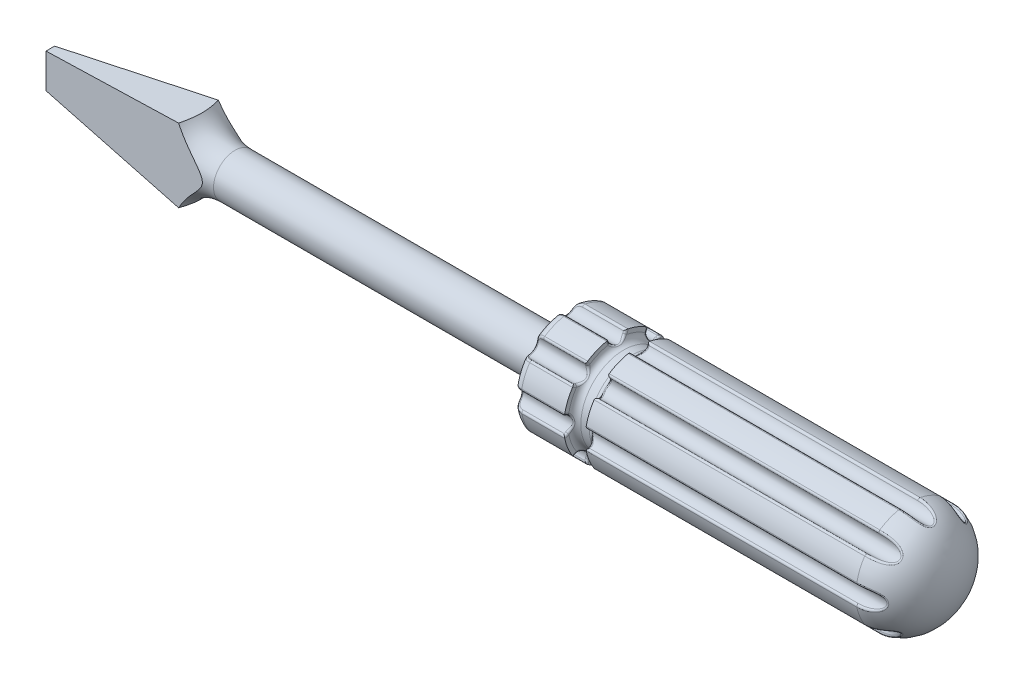
SolidWorks part; units mm, degrees
ref_plane "Front Plane" through (0, 0, 0) normal (0, 0, 1) x (1, 0, 0)
ref_plane "Top Plane" through (0, 0, 0) normal (0, 1, 0) x (1, 0, 0)
ref_plane "Right Plane" through (0, 0, 0) normal (1, 0, 0) x (0, 0, -1)
sketch "Sketch1" plane through (0, 0, 0) normal (0, 0, 1) x (1, 0, 0)
  line L0 (0, 0) -> (0, 8711.6046) construction
  line L1 (0, 0) -> (8711.6046, 0) construction
  line L2 (0, 0) -> (0, 5.25)
  line L3 (1, 6.25) -> (6, 6.25)
  line L4 (6, 6.25) -> (6, 5.75)
  line L5 (6.75, 5) -> (7.75, 5)
  line L6 (8.5, 5.75) -> (8.5, 6.25)
  line L7 (8.5, 6.25) -> (40, 6.25)
  line L8 (0, 0) -> (45, 0)
  arc A0 (7.75, 5) -> (8.5, 5.75) centre (7.75, 5.75) ccw
  arc A1 (6.75, 5) -> (6, 5.75) centre (6.75, 5.75) cw
  arc A2 (0, 5.25) -> (1, 6.25) centre (1, 5.25) cw
  ellipse E0 centre (40, 0) end of major axis (40, 6.25) minor radius 5 (45, 0) -> (40, 6.25) ccw
  point P20 (8.5, 5)
  point P23 (6, 5)
  point P26 (0, 6.25)
  dimension "D7" = 0.75
  dimension "D8" = 1
  dimension "D1" = 12.5
  dimension "D2" = 10
  dimension "D3" = 6
  dimension "D4" = 2.5
  dimension "D5" = 5
  dimension "D6" = 45
revolve "Revolve1" add sketch "Sketch1" angle 360 about L1
sketch "Sketch2" plane through (0, 0, 0) normal (-1, 0, 0) x (0, 0, 1)
  circle A0 centre (0, 0) radius 2.5
  dimension "D1" = 5
extrude "Boss-Extrude1" add sketch "Sketch2" along normal blind 43.5
sketch "Sketch3" plane through (0, 0, 0) normal (0, 0, 1) x (1, 0, 0)
  line L0 (0, 0) -> (-75.7303, 0) construction
  line L1 (0, 5.25) -> (0, -5.25) construction
  line L2 (-43.5, 2.5) -> (-43.5, -2.5) construction
  line L3 (-43.5, 8.25) -> (-60, 8.25)
  line L4 (-43.5, 8.25) -> (-43.5, -8.25)
  line L5 (-43.5, -8.25) -> (-60, -8.25)
  line L6 (-60, 8.25) -> (-60, -8.25)
  dimension "D1" = 16.5
extrude "Boss-Extrude2" add sketch "Sketch3" along normal mid plane 16.5
fillet "Fillet1" radius 5 1 edges at (-43.5, 0, 2.5)
sketch "Sketch4" plane through (0, 0, 8.25) normal (0, 0, 1) x (1, 0, 0)
  line L0 (-60, 0) -> (-50060, 0) construction
  line L1 (-60, 8.25) -> (-60, -8.25) construction
  line L2 (-60.0153, 0) -> (-60, 2)
  line L3 (-60, 2) -> (-42.3603, 4.3223)
  line L4 (-42.3603, 4.3223) -> (-42.3603, 8.25)
  line L5 (-42.3603, 8.25) -> (-60, 8.25)
  line L6 (-60, 8.25) -> (-60, 2)
  line L7 (-42.3603, -4.3223) -> (-42.3603, -8.25)
  line L8 (-60, -2) -> (-42.3603, -4.3223)
  line L9 (-60, -8.25) -> (-60, -2)
  line L10 (-42.3603, -8.25) -> (-60, -8.25)
  line L11 (-43.5, 8.25) -> (-60, 8.25) construction
  arc A0 (-43.5, 7.5) -> (-38.5, 2.5) centre (-38.5, 7.5) ccw construction
  point P4 (-60, 0)
  point P19 (0, 0)
  point P20 (0, 0)
  point P21 (0, 0)
  point P22 (0, 0)
  point P23 (0, 0)
  point P24 (0, 0)
  dimension "D1" = 4
  dimension "D2" = 15
extrude "Cut-Extrude4" cut sketch "Sketch4" against normal up to next contours L3 L4 L5 L6 | L7 L10 L9 L8
sketch "Sketch7" plane through (0, 0, 0) normal (0, 1, 0) x (1, 0, 0)
  line L0 (-60, 0) -> (-79.7831, 0) construction
  line L1 (-60, 8.25) -> (-60, -8.25) construction
  line L3 (-60, 0.5) -> (-39.6641, 2.6374)
  line L4 (-39.6641, 2.6374) -> (-39.6641, 8.25)
  line L5 (-39.6641, 8.25) -> (-60, 8.25)
  line L6 (-60, 8.25) -> (-60, 0.5)
  line L7 (-60, -8.25) -> (-60, -0.5)
  line L8 (-60, -0.5) -> (-39.6641, -2.6374)
  line L9 (-39.6641, -2.6374) -> (-39.6641, -8.25)
  line L10 (-39.6641, -8.25) -> (-60, -8.25)
  line L11 (-60, 8.25) -> (-43.5, 8.25) construction
  arc A0 (-43.5, 7.5) -> (-38.5, 2.5) centre (-38.5, 7.5) ccw construction
  dimension "D1" = 1
  dimension "D2" = 12
extrude "Cut-Extrude6" cut sketch "Sketch7" along normal through all both and the other way through all
sketch "Sketch9" plane through (0, 0, 0) normal (-1, 0, 0) x (0, 0, 1)
  circle A0 centre (0, 6.25) radius 1
  circle A1 centre (0, 0) radius 6.25 construction
  point P4 (0, 0)
  dimension "D1" = 2
extrude "Cut-Extrude7" cut sketch "Sketch9" against normal through all contours A0
fillet "Fillet2" radius 0.25 13 edges at (42.7123, 5.2504, -0.0283) (24.25, 6.17, -0.9968) (24.25, 6.17, 0.9968) (8.5, 5.9191, 0.9437) (8.5, 5.9191, -0.9437) (8.3215, 5.262, 0.1547) (6.1785, 5.262, -0.1547) (6, 5.9191, -0.9437) (6, 5.9191, 0.9437) (3.5, 6.17, -0.9968) (3.5, 6.17, 0.9968) (0.1628, 5.7334, 0.8562) (0.1646, 5.7359, -0.8577)
pattern_circular "CirPattern1" count 8 over 360 about axis through (-43.5, 0, 0) along (1, 0, 0) of "Cut-Extrude7", "Fillet2"
